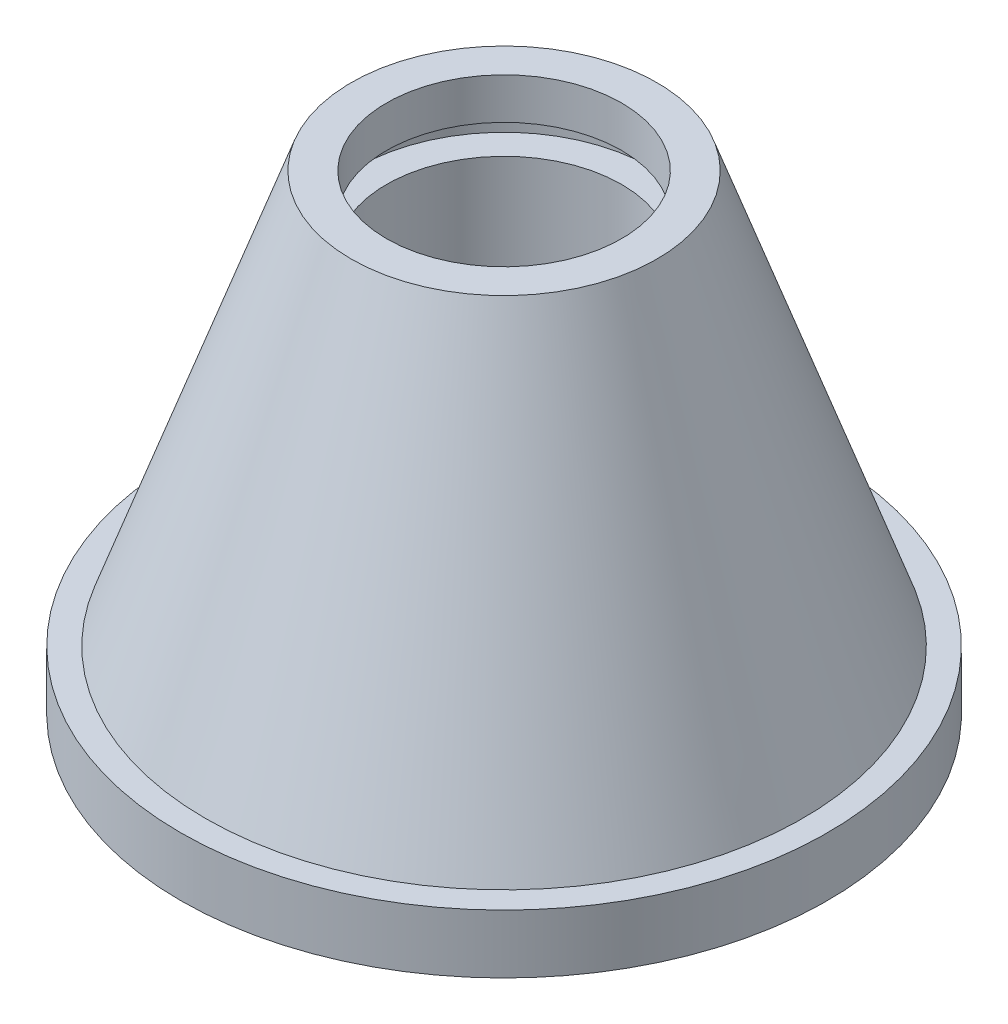
SolidWorks part; units mm, degrees
ref_plane "Front Plane" through (0, 0, 0) normal (0, 0, 1) x (1, 0, 0)
ref_plane "Top Plane" through (0, 0, 0) normal (0, 1, 0) x (1, 0, 0)
ref_plane "Right Plane" through (0, 0, 0) normal (1, 0, 0) x (0, 0, -1)
sketch "Sketch1" plane through (0, 0, 0) normal (0, 0, 1) x (1, 0, 0)
  line L0 (0, 128.2291) -> (0, -59.5164) construction
  line L1 (-113.8139, 0) -> (111.2044, 0) construction
  line L2 (-55, 0) -> (-35, 0)
  line L3 (-55, 0) -> (-55, 10)
  line L4 (-55, 10) -> (-50.7847, 10)
  line L5 (-50.7847, 10) -> (-26, 80)
  line L6 (-26, 80) -> (-20, 80)
  line L7 (-20, 80) -> (-20, 73)
  line L8 (-20, 73) -> (-25, 73)
  line L9 (-25, 73) -> (-25, 68)
  line L10 (-25, 68) -> (-20, 68)
  line L11 (-20, 68) -> (-20, 33)
  line L12 (-20, 33) -> (-35, 33)
  line L13 (-35, 33) -> (-35, 0)
  point P5 (-55, 5)
  point P7 (-52.8923, 10)
  point P19 (0, 128.2291)
  dimension "D1" = 55
  dimension "D2" = 35
  dimension "D3" = 20
  dimension "D4" = 25
  dimension "D5" = 20
  dimension "D6" = 33
  dimension "D7" = 5
  dimension "D8" = 7
  dimension "D9" = 80
  dimension "D10" = 10
  dimension "D11" = 35
  dimension "D12" = 26
  dimension "D13" = 74.2582
revolve "Revolve1" add sketch "Sketch1" angle 360 about L0
